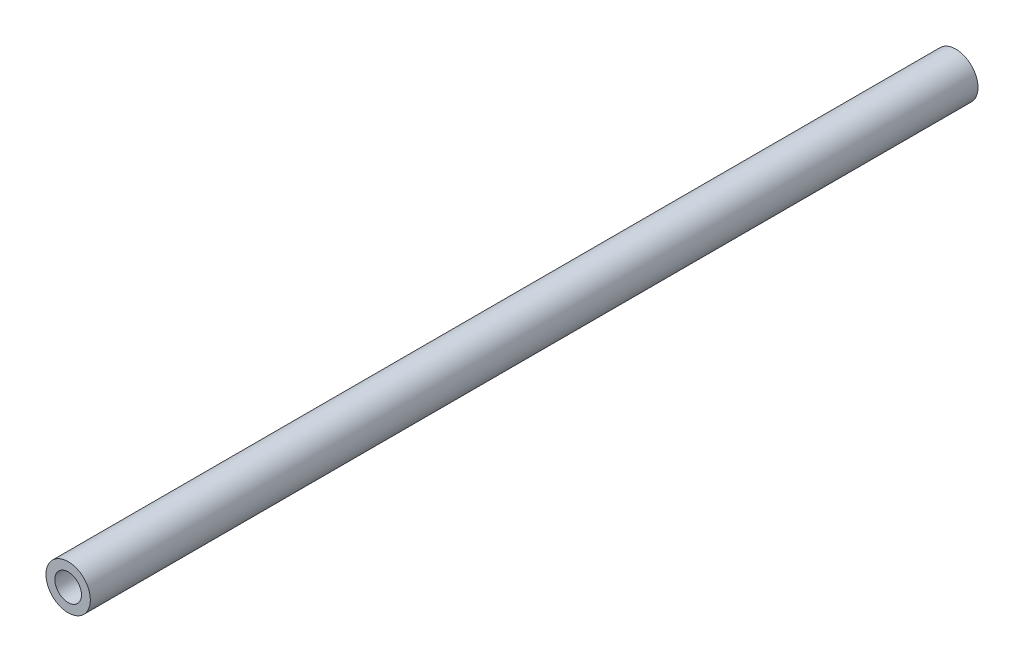
SolidWorks part; units mm, degrees
ref_plane "Front Plane" through (0, 0, 0) normal (0, 0, 1) x (1, 0, 0)
ref_plane "Top Plane" through (0, 0, 0) normal (0, 1, 0) x (1, 0, 0)
ref_plane "Right Plane" through (0, 0, 0) normal (1, 0, 0) x (0, 0, -1)
sketch "Sketch1" plane through (0, 0, 0) normal (0, 0, 1) x (1, 0, 0)
  circle A0 centre (0, 0) radius 7.5
  circle A1 centre (0, 0) radius 4.5
  dimension "D1" = 15
  dimension "D2" = 3
extrude "Boss-Extrude1" add sketch "Sketch1" along normal blind 300
